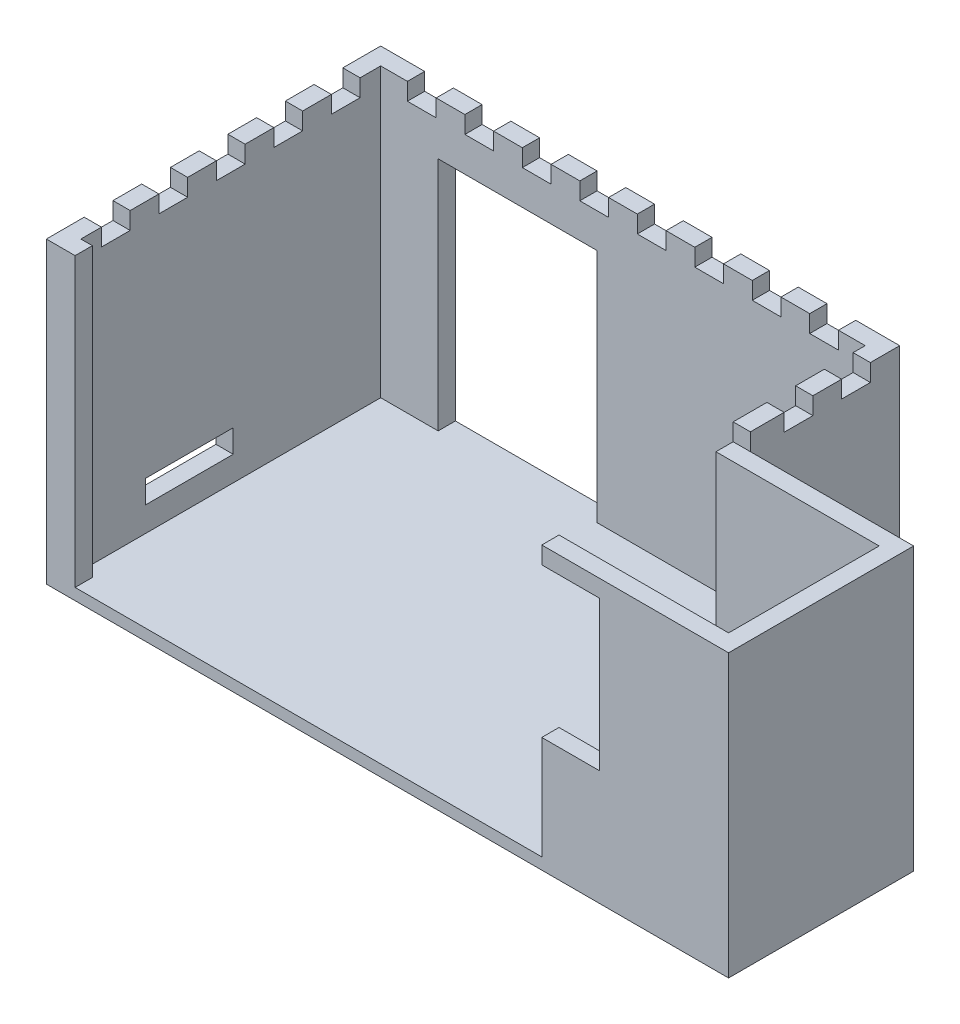
SolidWorks part; units mm, degrees
ref_plane "Front Plane" through (0, 0, 0) normal (0, 0, 1) x (1, 0, 0)
ref_plane "Top Plane" through (0, 0, 0) normal (0, 1, 0) x (1, 0, 0)
ref_plane "Right Plane" through (0, 0, 0) normal (1, 0, 0) x (0, 0, -1)
sketch "Sketch1" plane through (0, 0, 0) normal (0, 1, 0) x (1, 0, 0)
  line L1 (-36.501, 25.8398) -> (53.799, 25.8398)
  line L2 (-36.501, 25.8398) -> (-36.501, -32.3302)
  line L3 (-36.501, -32.3302) -> (53.799, -32.3302)
  line L4 (53.799, 25.8398) -> (53.799, -32.3302)
  dimension "D1" = 90.3
  dimension "D2" = 58.17
extrude "Boss-Extrude1" add sketch "Sketch1" along normal blind 2
sketch "Sketch4" plane through (0, 2, 0) normal (0, 1, 0) x (1, 0, 0)
  line L1 (53.799, -32.3302) -> (82.199, -32.3302)
  line L2 (53.799, -32.3302) -> (53.799, -0.1302)
  line L3 (53.799, -0.1302) -> (82.199, -0.1302)
  line L4 (82.199, -32.3302) -> (82.199, -0.1302)
  dimension "D1" = 28.4
  dimension "D2" = 32.2
extrude "Boss-Extrude2" add sketch "Sketch4" against normal blind 2 contours L4 L3 L2 L1
sketch "Sketch5" plane through (0, 2, 0) normal (0, 1, 0) x (1, 0, 0)
  line L0 (82.199, -0.1302) -> (82.199, -32.3302)
  line L1 (82.199, -32.3302) -> (49.699, -32.3302)
  line L2 (-36.501, -32.3302) -> (82.199, -32.3302) construction
  line L3 (49.699, -29.3302) -> (79.199, -29.3302)
  line L4 (79.199, -29.3302) -> (79.199, -3.1302)
  line L6 (49.699, -29.3302) -> (49.699, -32.3302)
  line L7 (82.199, -0.1302) -> (53.799, -0.1302)
  line L8 (53.799, -0.1302) -> (53.799, 25.8398)
  line L9 (53.799, 25.8398) -> (26.1553, 25.8398)
  line L10 (53.799, 25.8398) -> (-36.501, 25.8398) construction
  line L11 (26.1553, 25.8398) -> (26.1553, 22.8398)
  line L12 (26.1553, 22.8398) -> (50.799, 22.8398)
  line L13 (50.799, 22.8398) -> (50.799, -3.1302)
  line L14 (50.799, -3.1302) -> (79.199, -3.1302)
  point P10 (0, 0)
  dimension "D1" = 3
  dimension "D2" = 3
  dimension "D3" = 3
  dimension "D4" = 3
  dimension "D5" = 3
  dimension "D6" = 32.5
extrude "Boss-Extrude3" add sketch "Sketch5" along normal blind 20
sketch "Sketch6" plane through (0, 2, 0) normal (0, 1, 0) x (1, 0, 0)
  line L0 (-33.501, 25.8398) -> (-33.501, -32.3302)
  line L1 (26.1553, 25.8398) -> (-36.501, 25.8398) construction
  line L2 (-36.501, -32.3302) -> (49.699, -32.3302) construction
  line L3 (-33.501, -32.3302) -> (-36.501, -32.3302)
  line L4 (-36.501, -32.3302) -> (-36.501, 25.8398)
  line L5 (-36.501, 25.8398) -> (-33.501, 25.8398)
  dimension "D1" = 3
extrude "Boss-Extrude4" add sketch "Sketch6" along normal blind 50
sketch "Sketch7" plane through (-36.501, 0, 0) normal (-1, 0, 0) x (0, 0, 1)
  line L0 (32.3302, 52) -> (32.3302, 0) construction
  line L1 (2.8202, 6.31) -> (18.1202, 6.31)
  line L2 (2.8202, 6.31) -> (2.8202, 10.31)
  line L3 (2.8202, 10.31) -> (18.1202, 10.31)
  line L4 (18.1202, 6.31) -> (18.1202, 10.31)
  line L5 (-25.8398, 52) -> (-25.8398, 0) construction
  line L6 (-25.8398, 0) -> (32.3302, 0) construction
  dimension "D1" = 14.21
  dimension "D2" = 28.66
  dimension "D3" = 6.31
  dimension "D4" = 4
extrude "Cut-Extrude1" cut sketch "Sketch7" against normal blind 4 contours L2 L3 L4 L1
sketch "Sketch8" plane through (0, 2, 0) normal (0, 1, 0) x (1, 0, 0)
  line L1 (-33.501, 25.8398) -> (-23.501, 25.8398)
  line L2 (-33.501, 25.8398) -> (-33.501, 22.8398)
  line L3 (-33.501, 22.8398) -> (-23.501, 22.8398)
  line L4 (-23.501, 25.8398) -> (-23.501, 22.8398)
  line L5 (26.1553, 25.8398) -> (4.1553, 25.8398)
  line L6 (26.1553, 25.8398) -> (26.1553, 22.8398)
  line L7 (26.1553, 22.8398) -> (4.1553, 22.8398)
  line L8 (4.1553, 25.8398) -> (4.1553, 22.8398)
  dimension "D1" = 3
  dimension "D2" = 3
  dimension "D3" = 22
  dimension "D4" = 10
extrude "Boss-Extrude5" add sketch "Sketch8" along normal blind 50
sketch "Sketch9" plane through (4.1553, 0, 0) normal (-1, 0, 0) x (0, 0, 1)
  line L0 (-25.8398, 52) -> (-25.8398, 2) construction
  line L1 (-22.8398, 52) -> (-25.8398, 52)
  line L2 (-22.8398, 52) -> (-22.8398, 43)
  line L3 (-22.8398, 43) -> (-25.8398, 43)
  line L4 (-25.8398, 52) -> (-25.8398, 43)
  dimension "D1" = 9
extrude "Boss-Extrude7" add sketch "Sketch9" along normal blind 30 contours L4 L3 L2 L1
sketch "Sketch10" plane through (0, 22, 0) normal (0, 1, 0) x (1, 0, 0)
  line L0 (26.1553, 25.8398) -> (26.1553, 22.8398)
  line L1 (26.1553, 22.8398) -> (50.799, 22.8398)
  line L2 (50.799, 22.8398) -> (50.799, -3.1302)
  line L3 (50.799, -3.1302) -> (79.199, -3.1302)
  line L4 (79.199, -3.1302) -> (79.199, -29.3302)
  line L5 (79.199, -29.3302) -> (49.699, -29.3302)
  line L6 (49.699, -29.3302) -> (49.699, -32.3302)
  line L7 (49.699, -32.3302) -> (82.199, -32.3302)
  line L8 (49.699, -32.3302) -> (82.199, -32.3302) construction
  line L9 (82.199, -32.3302) -> (82.199, -0.1302) construction
  line L10 (82.199, -32.3302) -> (82.199, -0.1302)
  line L11 (82.199, -0.1302) -> (53.799, -0.1302)
  line L12 (53.799, -0.1302) -> (53.799, 25.8398)
  line L13 (53.799, 25.8398) -> (26.1553, 25.8398)
extrude "Boss-Extrude8" add sketch "Sketch10" along normal blind 30
sketch "Sketch11" plane through (0, 2, 0) normal (0, 1, 0) x (1, 0, 0)
  line L1 (-33.501, -32.3302) -> (-31.501, -32.3302)
  line L2 (-33.501, -32.3302) -> (-33.501, -29.3302)
  line L3 (-33.501, -29.3302) -> (-31.501, -29.3302)
  line L4 (-31.501, -32.3302) -> (-31.501, -29.3302)
  dimension "D1" = 3
  dimension "D2" = 2
extrude "Boss-Extrude9" add sketch "Sketch11" along normal blind 50
sketch "Sketch12" plane through (0, 0, 32.3302) normal (0, 0, 1) x (1, 0, 0)
  line L0 (49.699, 52) -> (49.699, 2) construction
  line L1 (49.699, 46) -> (59.699, 46)
  line L2 (49.699, 46) -> (49.699, 20)
  line L3 (49.699, 20) -> (59.699, 20)
  line L4 (59.699, 46) -> (59.699, 20)
  line L5 (49.699, 52) -> (82.199, 52) construction
  line L6 (-36.501, 0) -> (82.199, 0) construction
  dimension "D1" = 6
  dimension "D2" = 20
  dimension "D3" = 10
extrude "Cut-Extrude2" cut sketch "Sketch12" against normal blind 5
sketch "Sketch13" plane through (0, 52, 0) normal (0, 1, 0) x (1, 0, 0)
  line L0 (-36.501, 25.8398) -> (-36.501, -32.3302) construction
  line L1 (-36.501, -25.7452) -> (-33.501, -25.7452)
  line L2 (-36.501, -25.7452) -> (-36.501, -20.7452)
  line L3 (-36.501, -20.7452) -> (-33.501, -20.7452)
  line L4 (-33.501, -25.7452) -> (-33.501, -20.7452)
  line L5 (-33.501, -29.3302) -> (-33.501, 22.8398) construction
  line L6 (-36.501, -15.7452) -> (-36.501, -10.7452)
  line L7 (-36.501, -15.7452) -> (-33.501, -15.7452)
  line L8 (-33.501, -15.7452) -> (-33.501, -10.7452)
  line L9 (-36.501, -10.7452) -> (-33.501, -10.7452)
  line L10 (-36.501, -5.7452) -> (-36.501, -0.7452)
  line L11 (-36.501, -5.7452) -> (-33.501, -5.7452)
  line L12 (-33.501, -5.7452) -> (-33.501, -0.7452)
  line L13 (-36.501, -0.7452) -> (-33.501, -0.7452)
  line L14 (-36.501, 4.2548) -> (-36.501, 9.2548)
  line L15 (-36.501, 4.2548) -> (-33.501, 4.2548)
  line L16 (-33.501, 4.2548) -> (-33.501, 9.2548)
  line L17 (-36.501, 9.2548) -> (-33.501, 9.2548)
  line L18 (-36.501, 14.2548) -> (-36.501, 19.2548)
  line L19 (-36.501, 14.2548) -> (-33.501, 14.2548)
  line L20 (-33.501, 14.2548) -> (-33.501, 19.2548)
  line L21 (-36.501, 19.2548) -> (-33.501, 19.2548)
  line L22 (50.799, 22.8398) -> (50.799, -3.1302) construction
  line L23 (53.799, 25.8398) -> (-36.501, 25.8398) construction
  line L24 (-33.501, 22.8398) -> (50.799, 22.8398) construction
  line L25 (-28.851, 25.8398) -> (-23.851, 25.8398)
  line L26 (-28.851, 25.8398) -> (-28.851, 22.8398)
  line L27 (-28.851, 22.8398) -> (-23.851, 22.8398)
  line L28 (-23.851, 25.8398) -> (-23.851, 22.8398)
  line L29 (-18.851, 25.8398) -> (-18.851, 22.8398)
  line L30 (-18.851, 25.8398) -> (-13.851, 25.8398)
  line L31 (-13.851, 25.8398) -> (-13.851, 22.8398)
  line L32 (-18.851, 22.8398) -> (-13.851, 22.8398)
  line L33 (-8.851, 25.8398) -> (-8.851, 22.8398)
  line L34 (-8.851, 25.8398) -> (-3.851, 25.8398)
  line L35 (-3.851, 25.8398) -> (-3.851, 22.8398)
  line L36 (-8.851, 22.8398) -> (-3.851, 22.8398)
  line L37 (1.149, 25.8398) -> (1.149, 22.8398)
  line L38 (1.149, 25.8398) -> (6.149, 25.8398)
  line L39 (6.149, 25.8398) -> (6.149, 22.8398)
  line L40 (1.149, 22.8398) -> (6.149, 22.8398)
  line L41 (11.149, 25.8398) -> (11.149, 22.8398)
  line L42 (11.149, 25.8398) -> (16.149, 25.8398)
  line L43 (16.149, 25.8398) -> (16.149, 22.8398)
  line L44 (11.149, 22.8398) -> (16.149, 22.8398)
  line L45 (21.149, 25.8398) -> (21.149, 22.8398)
  line L46 (21.149, 25.8398) -> (26.149, 25.8398)
  line L47 (26.149, 25.8398) -> (26.149, 22.8398)
  line L48 (21.149, 22.8398) -> (26.149, 22.8398)
  line L49 (31.149, 25.8398) -> (31.149, 22.8398)
  line L50 (31.149, 25.8398) -> (36.149, 25.8398)
  line L51 (36.149, 25.8398) -> (36.149, 22.8398)
  line L52 (31.149, 22.8398) -> (36.149, 22.8398)
  line L53 (41.149, 25.8398) -> (41.149, 22.8398)
  line L54 (41.149, 25.8398) -> (46.149, 25.8398)
  line L55 (46.149, 25.8398) -> (46.149, 22.8398)
  line L56 (41.149, 22.8398) -> (46.149, 22.8398)
  line L57 (49.699, -32.3302) -> (82.199, -32.3302)
  line L58 (49.699, -32.3302) -> (49.699, -0.1302)
  line L59 (49.699, -0.1302) -> (82.199, -0.1302)
  line L60 (82.199, -32.3302) -> (82.199, -0.1302)
  line L61 (50.799, 20.7398) -> (53.799, 20.7398)
  line L62 (50.799, 20.7398) -> (50.799, 15.7398)
  line L63 (50.799, 15.7398) -> (53.799, 15.7398)
  line L64 (53.799, 20.7398) -> (53.799, 15.7398)
  line L65 (53.799, -0.1302) -> (53.799, 25.8398) construction
  line L66 (50.799, 10.7398) -> (50.799, 5.7398)
  line L67 (50.799, 10.7398) -> (53.799, 10.7398)
  line L68 (53.799, 10.7398) -> (53.799, 5.7398)
  line L69 (50.799, 5.7398) -> (53.799, 5.7398)
  line L70 (-63.0193, 25.8398) -> (-63.0193, -32.3302) construction
  line L71 (-36.501, 47.0156) -> (53.799, 47.0156) construction
  point P27 (-35.001, 14.2548)
  point P34 (-28.851, 24.3398)
  dimension "D1" = 6.585
  dimension "D2" = 5
  dimension "D4" = 5
  dimension "D5" = 6.585
  dimension "D6" = 5
  dimension "D8" = 5
  dimension "D9" = 7.65
  dimension "D10" = 7.65
  dimension "D11" = 5
  dimension "D13" = 58.17
  dimension "D14" = 90.3
  dimension "D15" = 5.1
  dimension "D16" = 5
  dimension "D3" = 5
  dimension "D7" = 8
  dimension "D12" = 2
extrude "Cut-Extrude3" cut sketch "Sketch13" against normal blind 3
